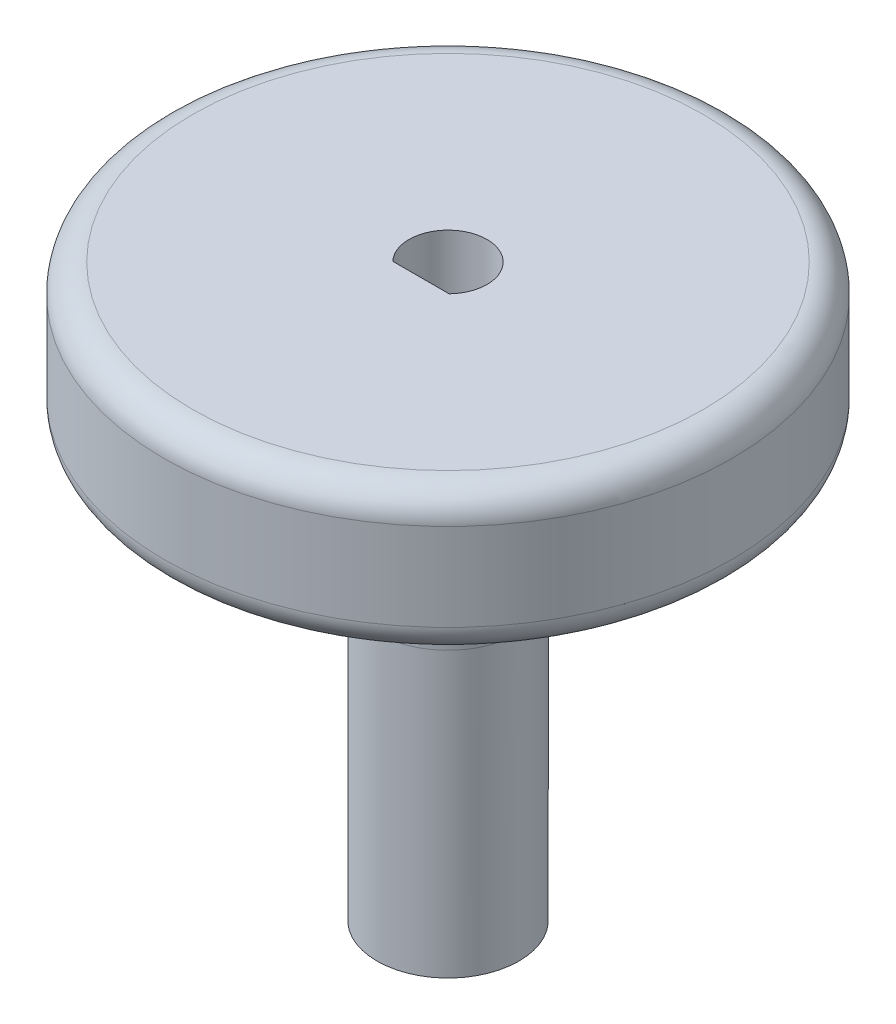
SolidWorks part; units mm, degrees
material "Cast Alloy Steel"
ref_plane "Front Plane" through (0, 0, 0) normal (0, 0, 1) x (1, 0, 0)
ref_plane "Top Plane" through (0, 0, 0) normal (0, 1, 0) x (1, 0, 0)
ref_plane "Right Plane" through (0, 0, 0) normal (1, 0, 0) x (0, 0, -1)
sketch "Sketch1" plane through (0, 0, 0) normal (0, 1, 0) x (1, 0, 0)
  circle A0 centre (0, 0) radius 20
  dimension "D1" = 40
extrude "Boss-Extrude1" add sketch "Sketch1" along normal blind 10.16
sketch "Sketch2" plane through (0, 10.16, 0) normal (0, 1, 0) x (1, 0, 0)
  line L0 (-0.889, 22.286) -> (0.889, 22.286) construction
  line L4 (-0.3175, 22.794) -> (0.3175, 22.794)
  line L5 (0, 22.794) -> (0, 20) construction
  line L6 (1.016, 21.905) -> (-1.016, 21.905) construction
  line L7 (1.016, 21.27) -> (-1.016, 21.27) construction
  line L8 (1.016, 20.508) -> (-1.016, 20.508) construction
  line L9 (1.4652, 19.7439) -> (1.7893, 18.1845) construction
  line L10 (1.7893, 18.1845) -> (0.5932, 18.1845) construction
  arc A7 (1.016, 20.508) -> (2.0879, 19.8907) centre (2.247, 21.4064) ccw
  arc A9 (-1.016, 20.508) -> (-2.0879, 19.8907) centre (-2.247, 21.4064) cw
  arc A10 (2.0879, 19.8907) -> (-2.0879, 19.8907) centre (0, 0) ccw
  circle A11 centre (0, 0) radius 20 construction
  spline S0 degree 3 poles (0.3175, 22.794) (0.6261, 22.794) (0.8624, 22.3936) (1.0586, 21.8364) (1.056, 21.2384) (0.8594, 20.7225) (1.016, 20.508) knots 0 0 0 0 0.257141 0.392199 0.605743 0.861996 0.861996 0.861996 0.861996
  spline S1 degree 3 poles (-0.3175, 22.794) (-0.6293, 22.794) (-0.8617, 22.3936) (-1.0588, 21.8364) (-1.0559, 21.2384) (-0.8594, 20.7225) (-1.016, 20.508) knots 0 0 0 0 0.257141 0.392199 0.605743 0.861996 0.861996 0.861996 0.861996
  point P2 (0, 21.905)
  point P17 (1.905, 25.3285)
  point P19 (0, 22.286)
  point P29 (0, 21.397)
  point P30 (0, 21.27)
  dimension "D3" = 0.889
  dimension "D4" = 2.286
  dimension "D8" = 1.524
  dimension "D1" = 0.3175
  dimension "D2" = 2.794
  dimension "D5" = 1.016
  dimension "D6" = 1.905
  dimension "D7" = 1.016
  dimension "D9" = 1.27
  dimension "D10" = 0.508
  dimension "D11" = 1.016
extrude "Boss-Extrude2" [suppressed] add sketch "Sketch2" against normal up to surface (10.16 mm away)
pattern_circular "CirPattern1" [suppressed] count 25 over 360
ref_point "Point1"
sketch "Sketch3" plane through (0, 0, 0) normal (0, -1, 0) x (1, 0, 0)
  circle A0 centre (0, 0) radius 5
  dimension "D1" = 10
extrude "Boss-Extrude3" add sketch "Sketch3" along normal blind 30
sketch "Sketch5" plane through (0, -30, 0) normal (0, -1, 0) x (1, 0, 0)
  line L0 (-1.9833, 1.905) -> (1.9833, 1.905)
  arc A0 (-1.9833, 1.905) -> (1.9833, 1.905) centre (0, 0) ccw
  dimension "D1" = 5.5
  dimension "D2" = 1.905
extrude "Cut-Extrude1" cut sketch "Sketch5" against normal up to surface (40.16 mm away) up to face at (0, 10.16, 20)
sketch "Sketch7" plane through (0, 0, 0) normal (0, -1, 0) x (1, 0, 0)
  circle A0 centre (0, 0) radius 9.525
  dimension "D1" = 19.05
extrude "Boss-Extrude4" [suppressed] add sketch "Sketch7" along normal blind 6.35 contours A0
fillet "Fillet1" radius 10 1 edges at (0, 0, -5)
fillet "Fillet2" radius 2 2 edges at (0, 10.16, 20) (0, 0, 20)
